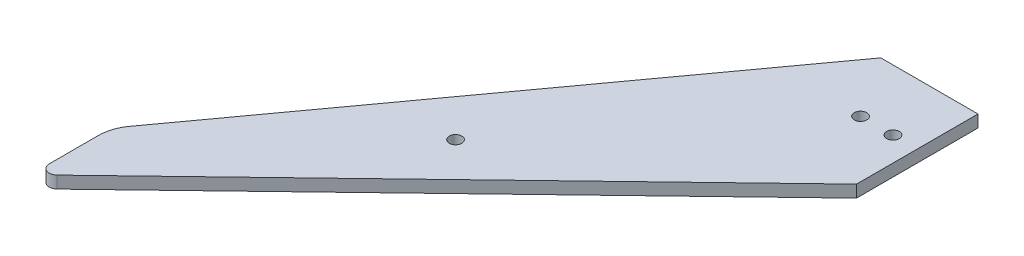
SolidWorks part; units mm, degrees
ref_plane "Front Plane" through (0, 0, 0) normal (0, 0, 1) x (1, 0, 0)
ref_plane "Top Plane" through (0, 0, 0) normal (0, 1, 0) x (1, 0, 0)
ref_plane "Right Plane" through (0, 0, 0) normal (1, 0, 0) x (0, 0, -1)
sketch "Sketch1" plane through (0, 0, 0) normal (0, 1, 0) x (1, 0, 0)
  line L0 (-12, 15) -> (-92, -95)
  line L1 (-12, -15) -> (12, -15)
  line L2 (-12, -15) -> (-12, 15)
  line L3 (-12, 15) -> (12, 15)
  line L4 (12, -15) -> (12, 15)
  line L5 (-12, -15) -> (12, 15) construction
  line L6 (-12, 15) -> (12, -15) construction
  line L7 (-92, -95) -> (-92, -115)
  line L8 (-92, -115) -> (12, -15)
  point P0 (0, 0)
  dimension "D1" = 30
  dimension "D2" = 24
  dimension "D3" = 80
  dimension "D4" = 100
  dimension "D5" = 20
extrude "Boss-Extrude1" add sketch "Sketch1" along normal mid plane 3 contours L7 L8 L1 L2 L0 | L1 L4 L3 L2
sketch "Sketch2" plane through (0, 1.5, 0) normal (0, 1, 0) x (1, 0, 0)
  line L0 (12, -15) -> (12, 15) construction
  circle A0 centre (6, 0) radius 1.55
  circle A1 centre (-2, 0) radius 1.55
  circle A2 centre (-47, -55) radius 1.55
  point P6 (0, 0)
  point P10 (-46.9501, -55.5758)
  dimension "D1" = 6
  dimension "D2" = 3.1
  dimension "D3" = 8
  dimension "D4" = 45
  dimension "D5" = 40
extrude "Cut-Extrude1" cut sketch "Sketch2" against normal up to surface (3 mm away) up to face at (-34.4, -1.5, 39)
fillet "Fillet1" radius 10 1 edges at (-92, 0, 95)
fillet "Fillet2" radius 2 1 edges at (-92, 0, 115)
